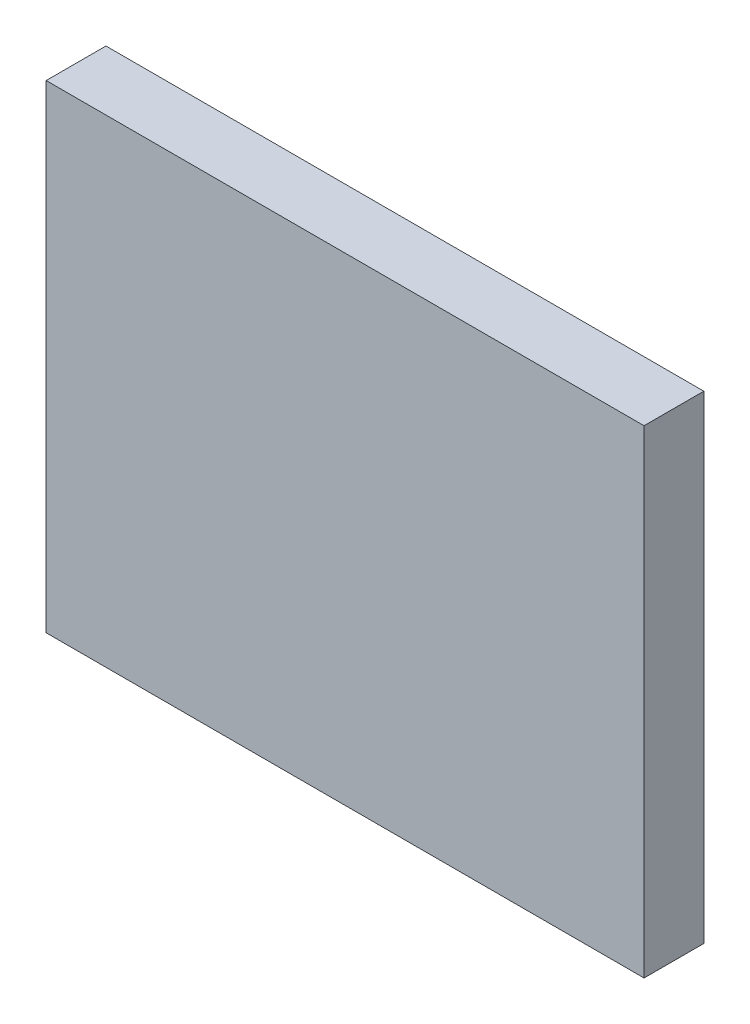
SolidWorks part; units mm, degrees
ref_plane "Front Plane" through (0, 0, 0) normal (0, 0, 1) x (1, 0, 0)
ref_plane "Top Plane" through (0, 0, 0) normal (0, 1, 0) x (1, 0, 0)
ref_plane "Right Plane" through (0, 0, 0) normal (1, 0, 0) x (0, 0, -1)
sketch "Sketch1" plane through (0, 0, 0) normal (0, 0, 1) x (1, 0, 0)
  line L1 (-20.5882, 9.2072) -> (29.4118, 9.2072)
  line L2 (-20.5882, 9.2072) -> (-20.5882, -30.7928)
  line L3 (-20.5882, -30.7928) -> (29.4118, -30.7928)
  line L4 (29.4118, 9.2072) -> (29.4118, -30.7928)
  dimension "D1" = 50
  dimension "D2" = 40
extrude "Boss-Extrude1" add sketch "Sketch1" along normal blind 5
